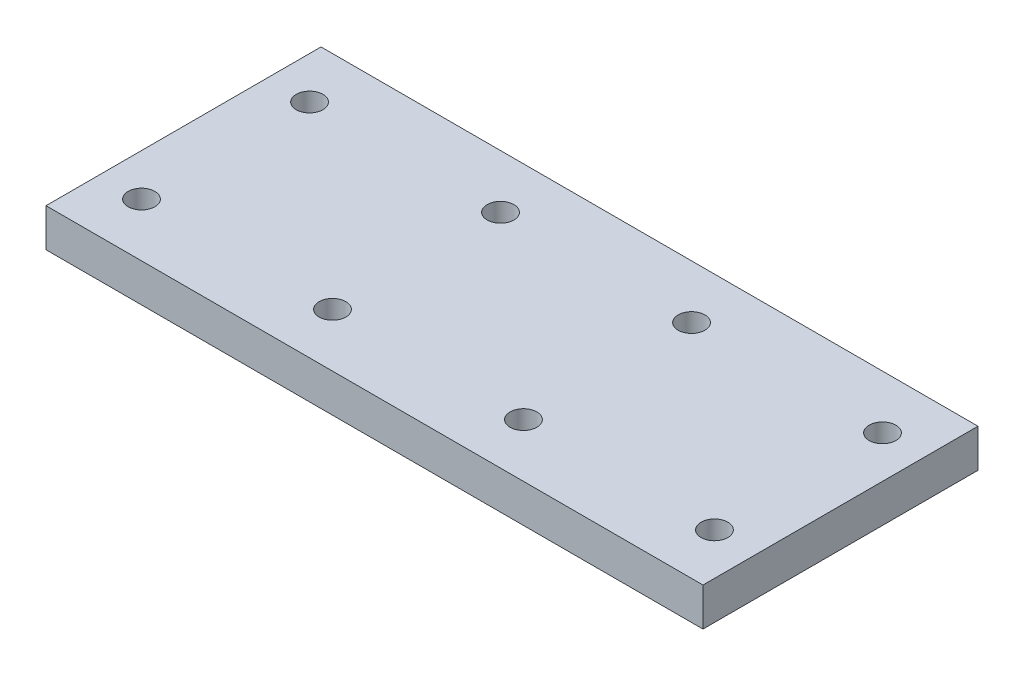
SolidWorks part; units mm, degrees
ref_plane "正面" through (0, 0, 0) normal (0, 0, 1) x (1, 0, 0)
ref_plane "平面" through (0, 0, 0) normal (0, 1, 0) x (1, 0, 0)
ref_plane "右側面" through (0, 0, 0) normal (1, 0, 0) x (0, 0, -1)
sketch "ｽｹｯﾁ1" plane through (0, 0, 0) normal (0, 1, 0) x (1, 0, 0)
  line L1 (-43, 18) -> (43, 18)
  line L2 (-43, 18) -> (-43, -18)
  line L3 (-43, -18) -> (43, -18)
  line L4 (43, 18) -> (43, -18)
  line L5 (-43, 18) -> (43, -18) construction
  line L6 (-43, -18) -> (43, 18) construction
  point P0 (0, 0)
  dimension "D1" = 36
  dimension "D2" = 86
extrude "ﾎﾞｽ - 押し出し1" add sketch "ｽｹｯﾁ1" along normal blind 5
sketch "ｽｹｯﾁ5" plane through (0, 5, 0) normal (0, 1, 0) x (1, 0, 0)
  line L1 (-8.7, -16.3) -> (-41.3, -16.3)
  line L2 (-8.7, -16.3) -> (-8.7, -5.7)
  line L3 (-8.7, -5.7) -> (-41.3, -5.7)
  line L4 (-41.3, -16.3) -> (-41.3, -5.7)
  line L5 (-8.7, -11) -> (-41.3, -11) construction
  line L6 (-25, -16.3) -> (-25, -5.7) construction
  line L7 (43, 0) -> (0, 0) construction
  line L8 (43, -18) -> (43, 18) construction
  line L9 (0, 0) -> (-70.4783, 0) construction
  line L10 (0, 0) -> (0, 18) construction
  line L11 (43, 18) -> (-43, 18) construction
  line L12 (-25, 16.3) -> (-25, 5.7) construction
  line L13 (-8.7, 11) -> (-41.3, 11) construction
  line L14 (-41.3, 16.3) -> (-41.3, 5.7)
  line L15 (-8.7, 5.7) -> (-41.3, 5.7)
  line L16 (-8.7, 16.3) -> (-8.7, 5.7)
  line L17 (-8.7, 16.3) -> (-41.3, 16.3)
  line L18 (8.7, 11) -> (41.3, 11) construction
  line L19 (25, 16.3) -> (25, 5.7) construction
  line L20 (25, -16.3) -> (25, -5.7) construction
  line L21 (8.7, -11) -> (41.3, -11) construction
  line L22 (8.7, 16.3) -> (41.3, 16.3)
  line L23 (8.7, 16.3) -> (8.7, 5.7)
  line L24 (8.7, 5.7) -> (41.3, 5.7)
  line L25 (41.3, 16.3) -> (41.3, 5.7)
  line L26 (41.3, -16.3) -> (41.3, -5.7)
  line L27 (8.7, -5.7) -> (41.3, -5.7)
  line L28 (8.7, -16.3) -> (8.7, -5.7)
  line L29 (8.7, -16.3) -> (41.3, -16.3)
  circle A0 centre (-37.5, -11) radius 1.75
  circle A1 centre (-12.5, -11) radius 1.75
  circle A2 centre (-12.5, 11) radius 1.75
  circle A3 centre (-37.5, 11) radius 1.75
  circle A4 centre (37.5, 11) radius 1.75
  circle A5 centre (12.5, 11) radius 1.75
  circle A6 centre (12.5, -11) radius 1.75
  circle A7 centre (37.5, -11) radius 1.75
  dimension "D5" = 3.5
  dimension "D7" = 3.8
  dimension "D1" = 10.6
  dimension "D2" = 32.6
  dimension "D3" = 11
  dimension "D4" = 12.5
  dimension "D6" = 0
extrude "ｶｯﾄ - 押し出し3" cut sketch "ｽｹｯﾁ5" against normal through all contours A7 | A6 | A4 | A5 | A2 | A1 | A0 | A3
